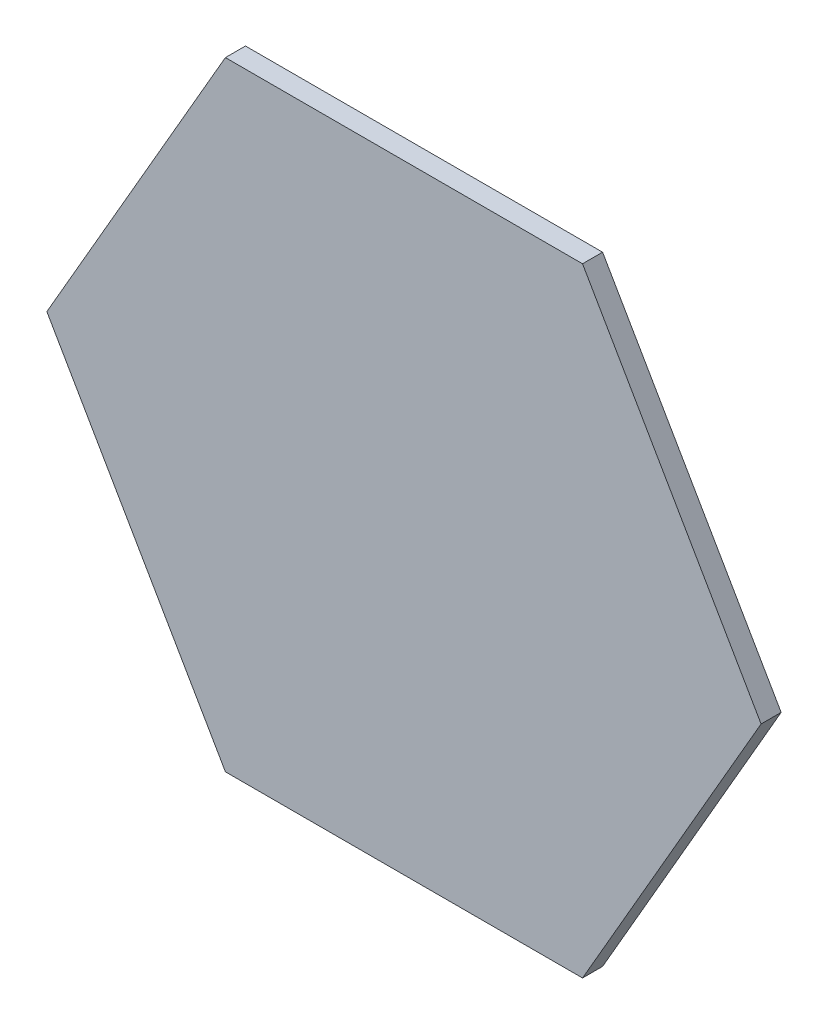
SolidWorks part; units mm, degrees
ref_plane "Front Plane" through (0, 0, 0) normal (0, 0, 1) x (1, 0, 0)
ref_plane "Top Plane" through (0, 0, 0) normal (0, 1, 0) x (1, 0, 0)
ref_plane "Right Plane" through (0, 0, 0) normal (1, 0, 0) x (0, 0, -1)
sketch "Sketch1" plane through (0, 0, 0) normal (0, 0, 1) x (1, 0, 0)
  line L1 (45.212, 0) -> (22.606, 39.1547)
  line L2 (22.606, 39.1547) -> (-22.606, 39.1547)
  line L3 (-22.606, 39.1547) -> (-45.212, 0)
  line L4 (-45.212, 0) -> (-22.606, -39.1547)
  line L5 (-22.606, -39.1547) -> (22.606, -39.1547)
  line L6 (22.606, -39.1547) -> (45.212, 0)
  circle A0 centre (0, 0) radius 39.1547 construction
  dimension "D1" = 45.212
extrude "Boss-Extrude1" add sketch "Sketch1" along normal blind 2.54 contours L1 L2 L3 L4 L5 L6
